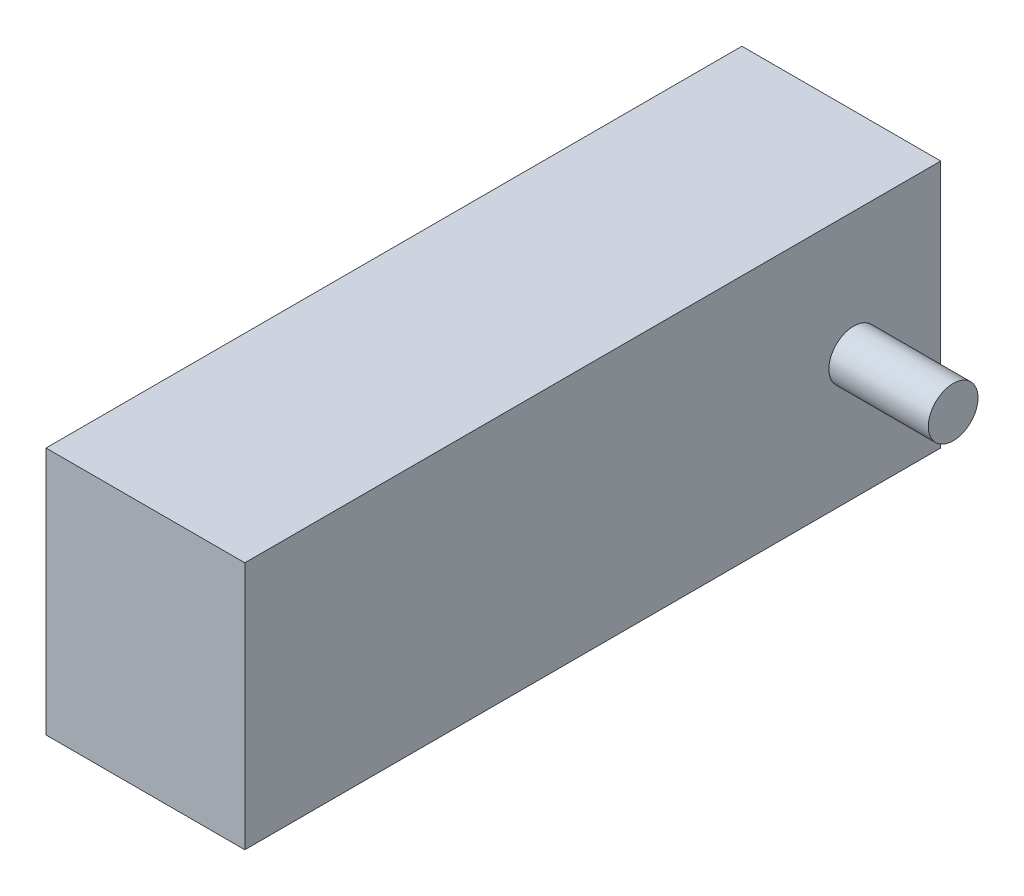
SolidWorks part; units mm, degrees
material "ABS"
ref_plane "Спереди" through (0, 0, 0) normal (0, 0, 1) x (1, 0, 0)
ref_plane "Сверху" through (0, 0, 0) normal (0, 1, 0) x (1, 0, 0)
ref_plane "Справа" through (0, 0, 0) normal (1, 0, 0) x (0, 0, -1)
sketch "Эскиз1" plane through (0, 0, 0) normal (0, 1, 0) x (1, 0, 0)
  line L1 (0, 0) -> (-20, 0)
  line L2 (0, 0) -> (0, 70)
  line L3 (0, 70) -> (-20, 70)
  line L4 (-20, 0) -> (-20, 70)
  dimension "D1" = 70
  dimension "D2" = 20
extrude "Корпус" add sketch "Эскиз1" along normal blind 25
sketch "Эскиз2" plane through (0, 0, 0) normal (1, 0, 0) x (0, 0, -1)
  line L0 (0, 25) -> (70, 25) construction
  line L1 (0, 0) -> (70, 0) construction
  line L2 (0, 25) -> (0, 0) construction
  line L3 (70, 25) -> (70, 0) construction
  circle A0 centre (61.25, 12.5) radius 2.5
  dimension "D3" = 5
  dimension "D4" = 61.25
  dimension "D5" = 8.75
  dimension "D1" = 12.5
  dimension "D2" = 12.5
extrude "Вал" add sketch "Эскиз2" along normal blind 10 and the other way blind 30
